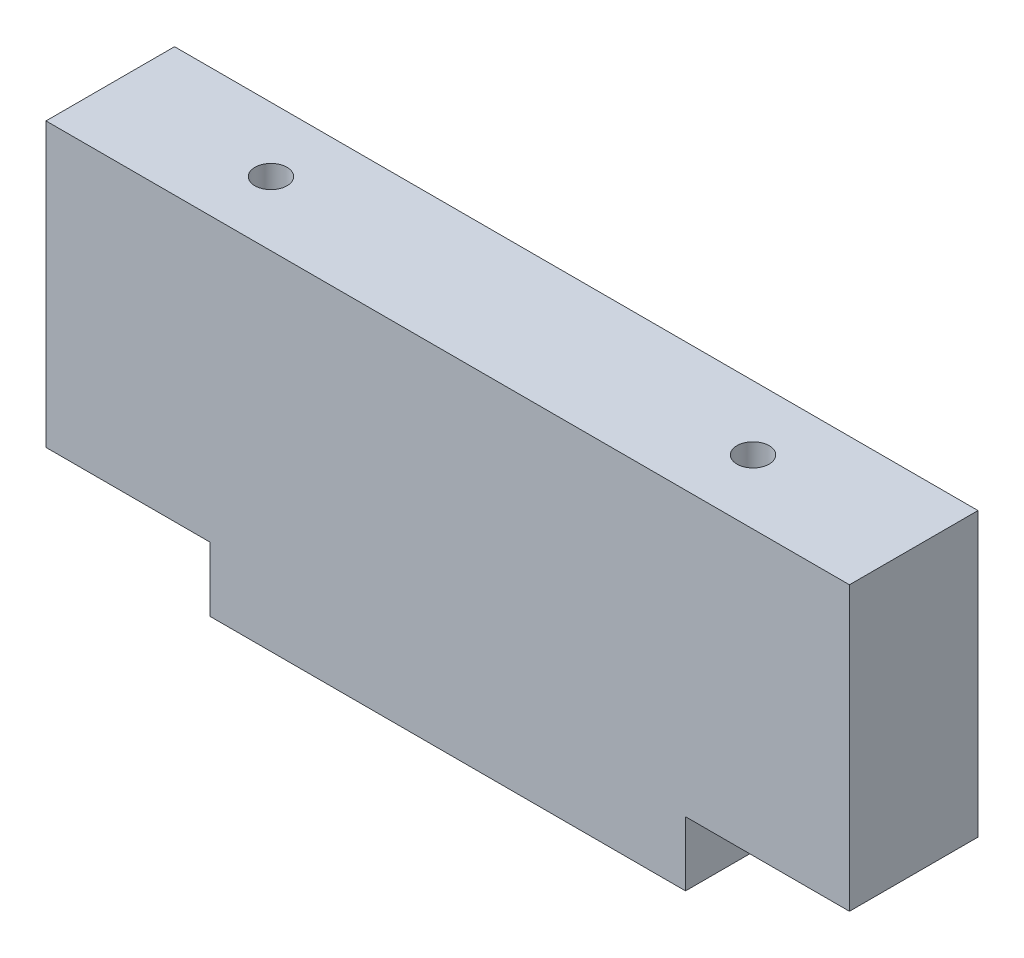
SolidWorks part; units mm, degrees
ref_plane "Front Plane" through (0, 0, 0) normal (0, 0, 1) x (1, 0, 0)
ref_plane "Top Plane" through (0, 0, 0) normal (0, 1, 0) x (1, 0, 0)
ref_plane "Right Plane" through (0, 0, 0) normal (1, 0, 0) x (0, 0, -1)
sketch "Sketch1" plane through (0, 0, 0) normal (0, 0, 1) x (1, 0, 0)
  line L0 (-37, 0) -> (37, 0)
  line L1 (37, 0) -> (37, 10)
  line L2 (37, 10) -> (62.5, 10)
  line L3 (62.5, 10) -> (62.5, 54)
  line L4 (62.5, 54) -> (-62.5, 54)
  line L5 (-62.5, 54) -> (-62.5, 10)
  line L6 (-62.5, 10) -> (-37, 10)
  line L7 (-37, 10) -> (-37, 0)
  point P4 (0, 0)
  dimension "D1" = 74
  dimension "D2" = 25.5
  dimension "D3" = 10
  dimension "D4" = 44
extrude "Boss-Extrude1" add sketch "Sketch1" along normal mid plane 20
hole_wizard "M6 Tapped Hole1" positions "Sketch2" profile "Sketch4" tap size "M6" standard "DIN"
sketch "Sketch2" plane through (0, 10, 0) normal (0, -1, 0) x (-1, 0, 0)
  line L0 (62.5, -10) -> (62.5, 10) construction
  point P0 (50, 0)
  point P2 (-50, 0)
  point P8 (47.9218, 0)
  dimension "D1" = 100
  dimension "D2" = 12.5
sketch "Sketch4" plane through (-50, 10, 0) normal (1, 0, 0) x (0, 0, -1)
  line L0 (0, 0) -> (0, 16.5022)
  line L1 (0, 16.5022) -> (2.5, 15)
  line L2 (2.5, 15) -> (2.5, 0)
  line L5 (2.5, 0) -> (0, 0)
  line L10 (0, 16.5022) -> (-2.5, 15) construction
  line L11 (0, -6.35) -> (0, 107.95) construction
  dimension "Tap Drill Dia." = 5
  dimension "Tap Drill Depth" = 15
  dimension "Drill Angle" = 118
cosmetic thread "Hole Thread1"
cosmetic thread "Hole Thread2"
hole_wizard "M6 Tapped Hole2" positions "Sketch5" profile "Sketch6" tap size "M6" standard "DIN"
sketch "Sketch5" plane through (0, 54, 0) normal (0, 1, 0) x (1, 0, 0)
  line L0 (-62.5, -10) -> (-62.5, 10) construction
  point P0 (-37.5, 0)
  point P2 (37.5, 0)
  point P5 (0, 0)
  dimension "D1" = 75
  dimension "D2" = 25
sketch "Sketch6" plane through (-37.5, 54, 0) normal (1, 0, 0) x (0, 0, 1)
  line L0 (0, 0) -> (0, 16.5022)
  line L1 (0, 16.5022) -> (2.5, 15)
  line L2 (2.5, 15) -> (2.5, 0)
  line L5 (2.5, 0) -> (0, 0)
  line L10 (0, 16.5022) -> (-2.5, 15) construction
  line L11 (0, -6.35) -> (0, 107.95) construction
  dimension "Tap Drill Dia." = 5
  dimension "Tap Drill Depth" = 15
  dimension "Drill Angle" = 118
cosmetic thread "Hole Thread3"
cosmetic thread "Hole Thread4"
